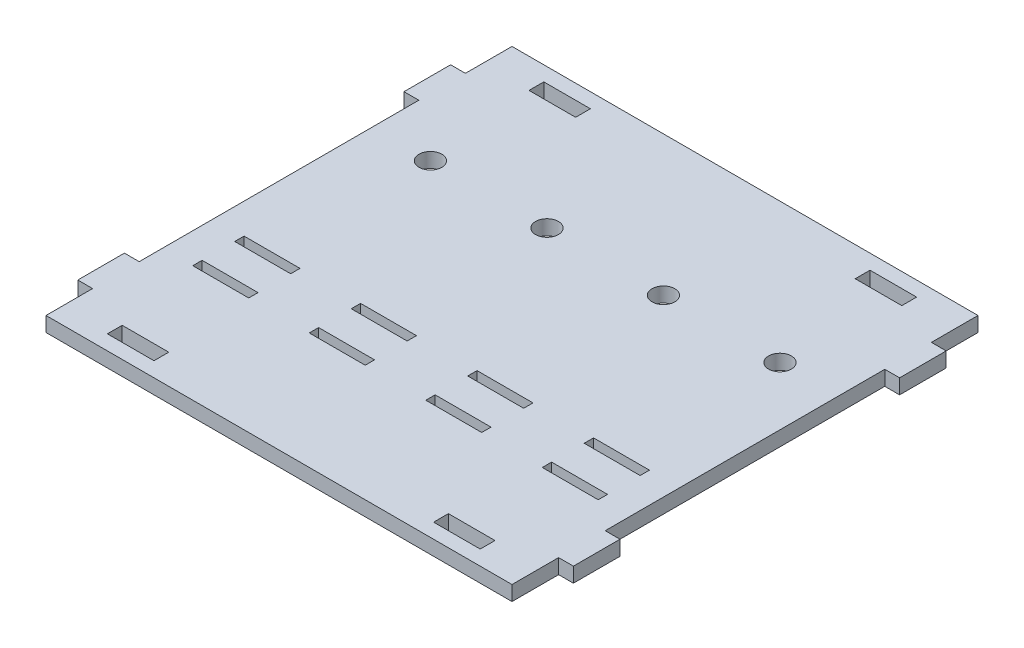
SolidWorks part; units mm, degrees
ref_plane "Front Plane" through (0, 0, 0) normal (0, 0, 1) x (1, 0, 0)
ref_plane "Top Plane" through (0, 0, 0) normal (0, 1, 0) x (1, 0, 0)
ref_plane "Right Plane" through (0, 0, 0) normal (1, 0, 0) x (0, 0, -1)
sketch "Sketch1" plane through (0, 0, 0) normal (0, 1, 0) x (1, 0, 0)
  line L0 (0, 50) -> (124.4476, 50) construction
  line L1 (0, 0) -> (100, 0)
  line L2 (0, 0) -> (0, 100) construction
  line L3 (0, 100) -> (100, 100)
  line L4 (100, 0) -> (100, 100) construction
  line L5 (10, 96.825) -> (20, 96.825)
  line L6 (10, 96.825) -> (10, 93.65)
  line L7 (10, 93.65) -> (20, 93.65)
  line L8 (20, 96.825) -> (20, 93.65)
  line L9 (80, 96.825) -> (90, 96.825)
  line L10 (80, 96.825) -> (80, 93.65)
  line L11 (80, 93.65) -> (90, 93.65)
  line L12 (90, 96.825) -> (90, 93.65)
  line L13 (90, 3.175) -> (90, 6.35)
  line L14 (80, 6.35) -> (90, 6.35)
  line L15 (80, 3.175) -> (80, 6.35)
  line L16 (80, 3.175) -> (90, 3.175)
  line L17 (20, 3.175) -> (20, 6.35)
  line L18 (10, 6.35) -> (20, 6.35)
  line L19 (10, 3.175) -> (10, 6.35)
  line L20 (10, 3.175) -> (20, 3.175)
  line L21 (0, 90) -> (0, 100)
  line L22 (0, 90) -> (-3.175, 90)
  line L23 (0, 80) -> (0, 20)
  line L24 (0, 80) -> (-3.175, 80)
  line L25 (-3.175, 90) -> (-3.175, 80)
  line L26 (50, 0) -> (50, 118.588) construction
  line L27 (0, 10) -> (0, 0)
  line L28 (-3.175, 10) -> (-3.175, 20)
  line L29 (0, 20) -> (-3.175, 20)
  line L30 (0, 10) -> (-3.175, 10)
  line L31 (100, 90) -> (100, 100)
  line L32 (100, 10) -> (103.175, 10)
  line L33 (100, 20) -> (103.175, 20)
  line L34 (103.175, 10) -> (103.175, 20)
  line L35 (100, 10) -> (100, 0)
  line L36 (103.175, 90) -> (103.175, 80)
  line L37 (100, 80) -> (103.175, 80)
  line L38 (100, 80) -> (100, 20)
  line L39 (100, 90) -> (103.175, 90)
  line L40 (31.5, 36) -> (43.5, 36)
  line L41 (6.5, 36) -> (18.5, 36)
  line L42 (6.5, 36) -> (6.5, 34)
  line L43 (6.5, 34) -> (18.5, 34)
  line L44 (18.5, 36) -> (18.5, 34)
  line L45 (6.5, 27) -> (18.5, 27)
  line L46 (6.5, 27) -> (6.5, 25)
  line L47 (6.5, 25) -> (18.5, 25)
  line L48 (18.5, 27) -> (18.5, 25)
  line L49 (31.5, 36) -> (31.5, 34)
  line L50 (31.5, 34) -> (43.5, 34)
  line L51 (43.5, 36) -> (43.5, 34)
  line L52 (31.5, 27) -> (43.5, 27)
  line L53 (31.5, 27) -> (31.5, 25)
  line L54 (31.5, 25) -> (43.5, 25)
  line L55 (43.5, 27) -> (43.5, 25)
  line L56 (56.5, 36) -> (68.5, 36)
  line L57 (56.5, 36) -> (56.5, 34)
  line L58 (56.5, 34) -> (68.5, 34)
  line L59 (68.5, 36) -> (68.5, 34)
  line L60 (56.5, 27) -> (68.5, 27)
  line L61 (56.5, 27) -> (56.5, 25)
  line L62 (56.5, 25) -> (68.5, 25)
  line L63 (68.5, 27) -> (68.5, 25)
  line L64 (81.5, 36) -> (93.5, 36)
  line L65 (81.5, 36) -> (81.5, 34)
  line L66 (81.5, 34) -> (93.5, 34)
  line L67 (93.5, 36) -> (93.5, 34)
  line L68 (81.5, 27) -> (93.5, 27)
  line L69 (81.5, 27) -> (81.5, 25)
  line L70 (81.5, 25) -> (93.5, 25)
  line L71 (93.5, 27) -> (93.5, 25)
  circle A0 centre (12.5, 70) radius 2.45
  circle A1 centre (37.5, 70) radius 2.45
  circle A2 centre (62.5, 70) radius 2.45
  circle A3 centre (87.5, 70) radius 2.45
  dimension "D13" = 4
  dimension "D14" = 12.5
  dimension "D15" = 30
  dimension "D16" = 12
  dimension "D23" = 4.9
  dimension "D1" = 100
  dimension "D2" = 100
  dimension "D3" = 10
  dimension "D4" = 10
  dimension "D5" = 3.175
  dimension "D6" = 3.175
  dimension "D7" = 10
  dimension "D8" = 10
  dimension "D9" = 3.175
  dimension "D10" = 3.175
  dimension "D11" = 10
  dimension "D12" = 10
  dimension "D17" = 2
  dimension "D18" = 2
  dimension "D19" = 12
  dimension "D20" = 7
  dimension "D21" = 6.5
  dimension "D22" = 25
extrude "Boss-Extrude1" add sketch "Sketch1" along normal blind 3.175
